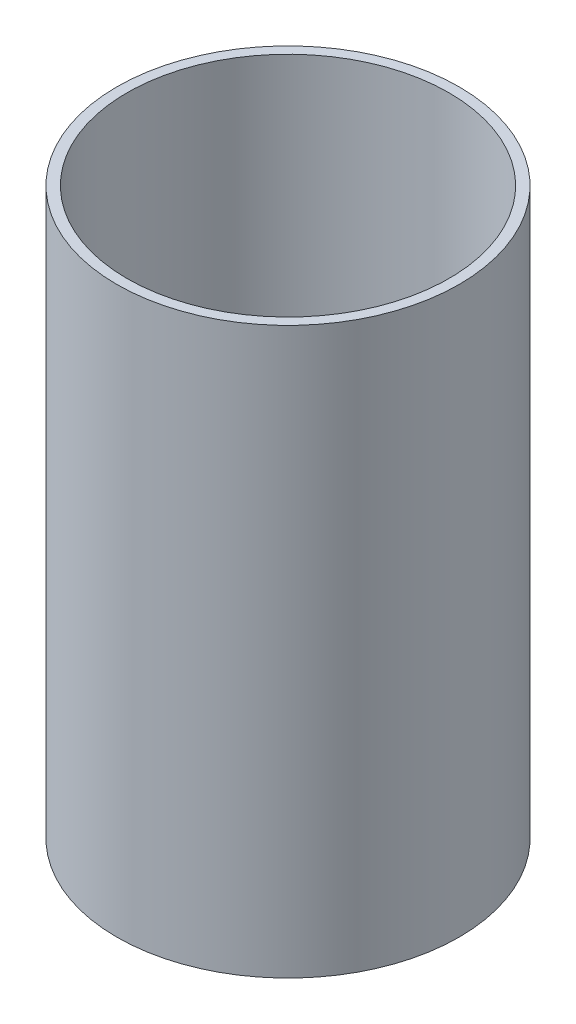
SolidWorks part; units mm, degrees
ref_plane "Front Plane" through (0, 0, 0) normal (0, 0, 1) x (1, 0, 0)
ref_plane "Top Plane" through (0, 0, 0) normal (0, 1, 0) x (1, 0, 0)
ref_plane "Right Plane" through (0, 0, 0) normal (1, 0, 0) x (0, 0, -1)
sketch "Sketch1" plane through (0, 0, 0) normal (0, 1, 0) x (1, 0, 0)
  circle A0 centre (0, 0) radius 25.175
  circle A1 centre (0, 0) radius 23.675
  dimension "D1" = 50.35
  dimension "D2" = 47.35
extrude "Boss-Extrude1" add sketch "Sketch1" along normal blind 83.14
